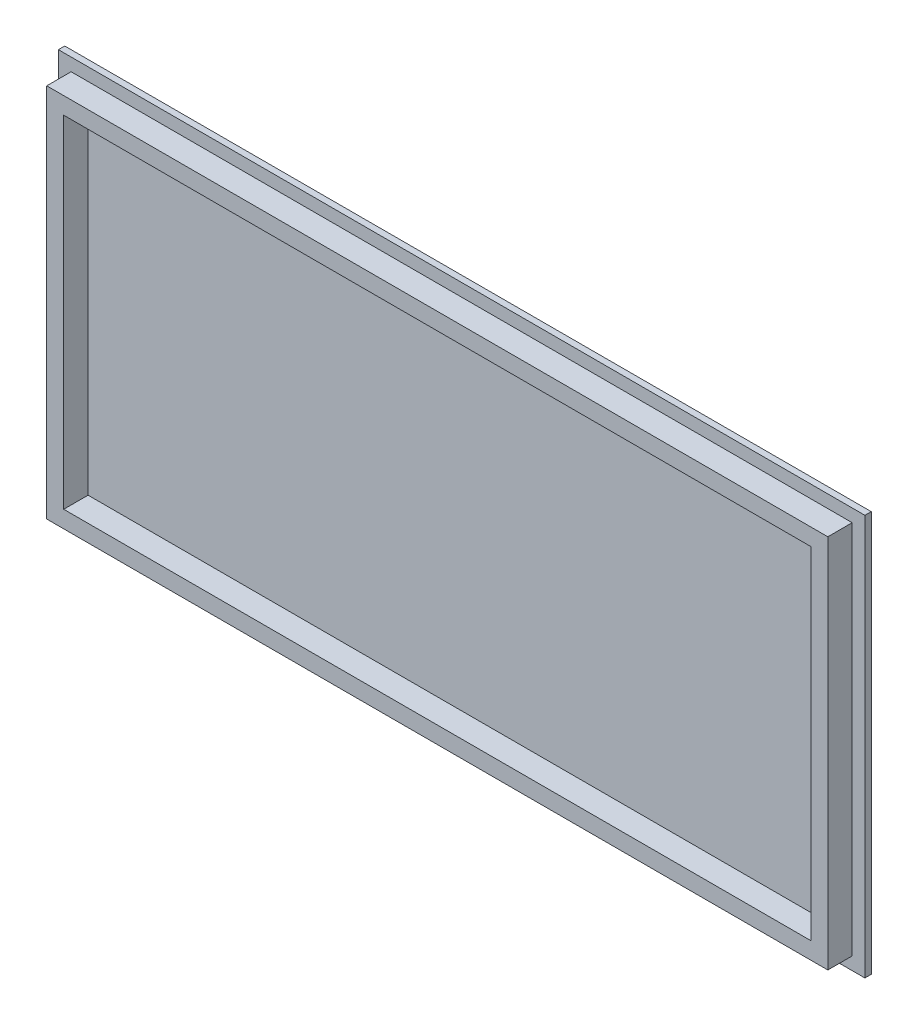
SolidWorks part; units mm, degrees
ref_plane "Front Plane" through (0, 0, 0) normal (0, 0, 1) x (1, 0, 0)
ref_plane "Top Plane" through (0, 0, 0) normal (0, 1, 0) x (1, 0, 0)
ref_plane "Right Plane" through (0, 0, 0) normal (1, 0, 0) x (0, 0, -1)
sketch "Model" plane through (0, 0, 0) normal (0, 0, 1) x (1, 0, 0)
  line L0 (3.8158, 5.1291) -> (3.565, 5.0023)
  line L1 (3.565, 5.0023) -> (3.3652, 4.8038)
  line L2 (3.3652, 4.8038) -> (3.2384, 4.5531)
  line L3 (3.2384, 4.5531) -> (3.1943, 4.2733)
  line L4 (3.1943, 4.2733) -> (3.2384, 3.9949)
  line L5 (3.2384, 3.9949) -> (3.3652, 3.7441)
  line L6 (3.3652, 3.7441) -> (3.565, 3.5457)
  line L7 (3.565, 3.5457) -> (3.8158, 3.4189)
  line L8 (3.8158, 3.4189) -> (4.0942, 3.3734)
  line L9 (4.0942, 3.3734) -> (4.3725, 3.4189)
  line L10 (4.3725, 3.4189) -> (4.6233, 3.5457)
  line L11 (4.6233, 3.5457) -> (4.8231, 3.7441)
  line L12 (4.8231, 3.7441) -> (4.9499, 3.9949)
  line L13 (4.9499, 3.9949) -> (4.994, 4.2733)
  line L14 (4.994, 4.2733) -> (4.9499, 4.5531)
  line L15 (4.9499, 4.5531) -> (4.8231, 4.8038)
  line L16 (4.8231, 4.8038) -> (4.6233, 5.0023)
  line L17 (4.6233, 5.0023) -> (4.3725, 5.1291)
  line L18 (4.3725, 5.1291) -> (4.0942, 5.1732)
  line L19 (4.0942, 5.1732) -> (3.8158, 5.1291)
  line L20 (75.7107, 5.1291) -> (75.4599, 5.0023)
  line L21 (75.4599, 5.0023) -> (75.2602, 4.8038)
  line L22 (75.2602, 4.8038) -> (75.1321, 4.5531)
  line L23 (75.1321, 4.5531) -> (75.088, 4.2733)
  line L24 (75.088, 4.2733) -> (75.1321, 3.9949)
  line L25 (75.1321, 3.9949) -> (75.2602, 3.7441)
  line L26 (75.2602, 3.7441) -> (75.4599, 3.5457)
  line L27 (75.4599, 3.5457) -> (75.7107, 3.4189)
  line L28 (75.7107, 3.4189) -> (75.989, 3.3734)
  line L29 (75.989, 3.3734) -> (76.2663, 3.4189)
  line L30 (76.2663, 3.4189) -> (76.5168, 3.5457)
  line L31 (76.5168, 3.5457) -> (76.7168, 3.7441)
  line L32 (76.7168, 3.7441) -> (76.8449, 3.9949)
  line L33 (76.8449, 3.9949) -> (76.889, 4.2733)
  line L34 (76.889, 4.2733) -> (76.8449, 4.5531)
  line L35 (76.8449, 4.5531) -> (76.7168, 4.8038)
  line L36 (76.7168, 4.8038) -> (76.5168, 5.0023)
  line L37 (76.5168, 5.0023) -> (76.2663, 5.1291)
  line L38 (76.2663, 5.1291) -> (75.989, 5.1732)
  line L39 (75.989, 5.1732) -> (75.7107, 5.1291)
  line L40 (147.606, 5.1291) -> (147.355, 5.0023)
  line L41 (147.355, 5.0023) -> (147.155, 4.8038)
  line L42 (147.155, 4.8038) -> (147.027, 4.5531)
  line L43 (147.027, 4.5531) -> (146.983, 4.2733)
  line L44 (146.983, 4.2733) -> (147.027, 3.9949)
  line L45 (147.027, 3.9949) -> (147.155, 3.7441)
  line L46 (147.155, 3.7441) -> (147.355, 3.5457)
  line L47 (147.355, 3.5457) -> (147.606, 3.4189)
  line L48 (147.606, 3.4189) -> (147.884, 3.3734)
  line L49 (147.884, 3.3734) -> (148.161, 3.4189)
  line L50 (148.161, 3.4189) -> (148.412, 3.5457)
  line L51 (148.412, 3.5457) -> (148.612, 3.7441)
  line L52 (148.612, 3.7441) -> (148.74, 3.9949)
  line L53 (148.74, 3.9949) -> (148.784, 4.2733)
  line L54 (148.784, 4.2733) -> (148.74, 4.5531)
  line L55 (148.74, 4.5531) -> (148.612, 4.8038)
  line L56 (148.612, 4.8038) -> (148.412, 5.0023)
  line L57 (148.412, 5.0023) -> (148.161, 5.1291)
  line L58 (148.161, 5.1291) -> (147.884, 5.1732)
  line L59 (147.884, 5.1732) -> (147.606, 5.1291)
  line L60 (219.499, 5.1291) -> (219.25, 5.0023)
  line L61 (219.25, 5.0023) -> (219.049, 4.8038)
  line L62 (219.049, 4.8038) -> (218.922, 4.5531)
  line L63 (218.922, 4.5531) -> (218.878, 4.2733)
  line L64 (218.878, 4.2733) -> (218.922, 3.9949)
  line L65 (218.922, 3.9949) -> (219.049, 3.7441)
  line L66 (219.049, 3.7441) -> (219.25, 3.5457)
  line L67 (219.25, 3.5457) -> (219.499, 3.4189)
  line L68 (219.499, 3.4189) -> (219.778, 3.3734)
  line L69 (219.778, 3.3734) -> (220.056, 3.4189)
  line L70 (220.056, 3.4189) -> (220.307, 3.5457)
  line L71 (220.307, 3.5457) -> (220.507, 3.7441)
  line L72 (220.507, 3.7441) -> (220.635, 3.9949)
  line L73 (220.635, 3.9949) -> (220.679, 4.2733)
  line L74 (220.679, 4.2733) -> (220.635, 4.5531)
  line L75 (220.635, 4.5531) -> (220.507, 4.8038)
  line L76 (220.507, 4.8038) -> (220.307, 5.0023)
  line L77 (220.307, 5.0023) -> (220.056, 5.1291)
  line L78 (220.056, 5.1291) -> (219.778, 5.1732)
  line L79 (219.778, 5.1732) -> (219.499, 5.1291)
  line L80 (291.394, 5.1291) -> (291.144, 5.0023)
  line L81 (291.144, 5.0023) -> (290.944, 4.8038)
  line L82 (290.944, 4.8038) -> (290.817, 4.5531)
  line L83 (290.817, 4.5531) -> (290.773, 4.2733)
  line L84 (290.773, 4.2733) -> (290.817, 3.9949)
  line L85 (290.817, 3.9949) -> (290.944, 3.7441)
  line L86 (290.944, 3.7441) -> (291.144, 3.5457)
  line L87 (291.144, 3.5457) -> (291.394, 3.4189)
  line L88 (291.394, 3.4189) -> (291.673, 3.3734)
  line L89 (291.673, 3.3734) -> (291.95, 3.4189)
  line L90 (291.95, 3.4189) -> (292.202, 3.5457)
  line L91 (292.202, 3.5457) -> (292.401, 3.7441)
  line L92 (292.401, 3.7441) -> (292.529, 3.9949)
  line L93 (292.529, 3.9949) -> (292.573, 4.2733)
  line L94 (292.573, 4.2733) -> (292.529, 4.5531)
  line L95 (292.529, 4.5531) -> (292.401, 4.8038)
  line L96 (292.401, 4.8038) -> (292.202, 5.0023)
  line L97 (292.202, 5.0023) -> (291.95, 5.1291)
  line L98 (291.95, 5.1291) -> (291.673, 5.1732)
  line L99 (291.673, 5.1732) -> (291.394, 5.1291)
  line L100 (363.291, 5.1291) -> (363.04, 5.0023)
  line L101 (363.04, 5.0023) -> (362.839, 4.8038)
  line L102 (362.839, 4.8038) -> (362.712, 4.5531)
  line L103 (362.712, 4.5531) -> (362.67, 4.2733)
  line L104 (362.67, 4.2733) -> (362.712, 3.9949)
  line L105 (362.712, 3.9949) -> (362.839, 3.7441)
  line L106 (362.839, 3.7441) -> (363.04, 3.5457)
  line L107 (363.04, 3.5457) -> (363.291, 3.4189)
  line L108 (363.291, 3.4189) -> (363.569, 3.3734)
  line L109 (363.569, 3.3734) -> (363.844, 3.4189)
  line L110 (363.844, 3.4189) -> (364.098, 3.5457)
  line L111 (364.098, 3.5457) -> (364.296, 3.7441)
  line L112 (364.296, 3.7441) -> (364.423, 3.9949)
  line L113 (364.423, 3.9949) -> (364.469, 4.2733)
  line L114 (364.469, 4.2733) -> (364.423, 4.5531)
  line L115 (364.423, 4.5531) -> (364.296, 4.8038)
  line L116 (364.296, 4.8038) -> (364.098, 5.0023)
  line L117 (364.098, 5.0023) -> (363.844, 5.1291)
  line L118 (363.844, 5.1291) -> (363.569, 5.1732)
  line L119 (363.569, 5.1732) -> (363.291, 5.1291)
  line L120 (131.917, 27.3251) -> (189.071, 27.3251)
  line L121 (189.071, 27.3251) -> (189.071, 8.2737)
  line L122 (189.071, 8.2737) -> (131.917, 8.2737)
  line L123 (131.917, 8.2737) -> (131.917, 27.3251)
  line L124 (250.028, 142.579) -> (250.028, 123.963)
  line L125 (250.028, 123.963) -> (246.976, 138.322)
  line L126 (246.976, 138.322) -> (228.342, 134.36)
  line L127 (228.342, 134.36) -> (228.342, 134.361)
  line L128 (228.342, 134.361) -> (209.708, 130.4)
  line L129 (209.708, 130.4) -> (209.708, 130.401)
  line L130 (209.708, 130.401) -> (172.44, 122.479)
  line L131 (172.44, 122.479) -> (176.4, 103.845)
  line L132 (176.4, 103.845) -> (167.083, 101.865)
  line L133 (167.083, 101.865) -> (171.045, 83.228)
  line L134 (171.045, 83.228) -> (175.703, 84.2186)
  line L135 (175.703, 84.2186) -> (179.663, 65.5863)
  line L136 (179.663, 65.5863) -> (165.687, 62.6166)
  line L137 (165.687, 62.6166) -> (169.649, 43.9801)
  line L138 (169.649, 43.9801) -> (178.966, 45.9617)
  line L139 (178.966, 45.9617) -> (182.926, 27.3279)
  line L140 (182.926, 27.3279) -> (243.487, 40.2001)
  line L141 (243.487, 40.2001) -> (243.487, 40.1987)
  line L142 (243.487, 40.1987) -> (266.78, 45.1513)
  line L143 (266.78, 45.1513) -> (258.859, 82.4205)
  line L144 (258.859, 82.4205) -> (254.2, 81.431)
  line L145 (254.2, 81.431) -> (250.241, 100.062)
  line L146 (250.241, 100.062) -> (254.791, 101.03)
  line L147 (254.791, 101.03) -> (254.791, 82.568)
  line L148 (254.791, 82.568) -> (264.316, 82.568)
  line L149 (264.316, 82.568) -> (264.316, 63.518)
  line L150 (264.316, 63.518) -> (270.031, 63.518)
  line L151 (270.031, 63.518) -> (270.031, 44.468)
  line L152 (270.031, 44.468) -> (293.846, 44.468)
  line L153 (293.846, 44.468) -> (293.846, 63.518)
  line L154 (293.846, 63.518) -> (316.705, 63.518)
  line L155 (316.705, 63.518) -> (316.705, 82.568)
  line L156 (316.705, 82.568) -> (335.755, 82.568)
  line L157 (335.755, 82.568) -> (335.755, 101.621)
  line L158 (335.755, 101.621) -> (330.992, 101.621)
  line L159 (330.992, 101.621) -> (330.992, 120.671)
  line L160 (330.992, 120.671) -> (326.23, 120.671)
  line L161 (326.23, 120.671) -> (326.23, 139.721)
  line L162 (326.23, 139.721) -> (269.08, 139.721)
  line L163 (269.08, 139.721) -> (269.08, 142.579)
  line L164 (269.08, 142.579) -> (250.028, 142.579)
  line L165 (79.6452, 120.831) -> (70.327, 122.811)
  line L166 (70.327, 122.811) -> (66.3663, 104.176)
  line L167 (66.3663, 104.176) -> (71.0255, 103.185)
  line L168 (71.0255, 103.185) -> (67.0648, 84.551)
  line L169 (67.0648, 84.551) -> (76.382, 82.5722)
  line L170 (76.382, 82.5722) -> (72.42, 63.9367)
  line L171 (72.42, 63.9367) -> (72.4214, 63.9367)
  line L172 (72.4214, 63.9367) -> (68.4597, 45.303)
  line L173 (68.4597, 45.303) -> (133.679, 31.4399)
  line L174 (133.679, 31.4399) -> (133.679, 31.4413)
  line L175 (133.679, 31.4413) -> (152.313, 27.4808)
  line L176 (152.313, 27.4808) -> (156.275, 46.1162)
  line L177 (156.275, 46.1162) -> (146.958, 48.0949)
  line L178 (146.958, 48.0949) -> (150.919, 66.7286)
  line L179 (150.919, 66.7286) -> (141.602, 68.7091)
  line L180 (141.602, 68.7091) -> (145.562, 87.3428)
  line L181 (145.562, 87.3428) -> (140.903, 88.3338)
  line L182 (140.903, 88.3338) -> (144.865, 106.966)
  line L183 (144.865, 106.966) -> (154.182, 104.986)
  line L184 (154.182, 104.986) -> (158.142, 123.621)
  line L185 (158.142, 123.621) -> (139.507, 127.583)
  line L186 (139.507, 127.583) -> (139.507, 127.581)
  line L187 (139.507, 127.581) -> (83.6055, 139.464)
  line L188 (83.6055, 139.464) -> (79.6452, 120.831)
  line L189 (321.466, 77.8083) -> (321.466, 58.7583)
  line L190 (321.466, 58.7583) -> (302.416, 58.7583)
  line L191 (302.416, 58.7583) -> (302.416, 39.7069)
  line L192 (302.416, 39.7069) -> (359.569, 39.7069)
  line L193 (359.569, 39.7069) -> (359.569, 58.7583)
  line L194 (359.569, 58.7583) -> (340.517, 58.7583)
  line L195 (340.517, 58.7583) -> (340.517, 77.8083)
  line L196 (340.517, 77.8083) -> (321.466, 77.8083)
  line L197 (60.4795, 142.579) -> (60.4795, 139.721)
  line L198 (60.4795, 139.721) -> (22.3807, 139.721)
  line L199 (22.3807, 139.721) -> (22.3807, 120.671)
  line L200 (22.3807, 120.671) -> (17.6182, 120.671)
  line L201 (17.6182, 120.671) -> (17.6182, 101.621)
  line L202 (17.6182, 101.621) -> (12.8557, 101.621)
  line L203 (12.8557, 101.621) -> (12.8557, 82.5708)
  line L204 (12.8557, 82.5708) -> (8.0932, 82.5708)
  line L205 (8.0932, 82.5708) -> (8.0932, 44.468)
  line L206 (8.0932, 44.468) -> (60.482, 44.468)
  line L207 (60.482, 44.468) -> (60.482, 63.518)
  line L208 (60.482, 63.518) -> (70.007, 63.518)
  line L209 (70.007, 63.518) -> (70.007, 82.5708)
  line L210 (70.007, 82.5708) -> (65.2459, 82.5708)
  line L211 (65.2459, 82.5708) -> (65.2459, 120.671)
  line L212 (65.2459, 120.671) -> (60.482, 120.671)
  line L213 (60.482, 120.671) -> (60.482, 123.526)
  line L214 (60.482, 123.526) -> (79.532, 123.526)
  line L215 (79.532, 123.526) -> (79.532, 142.579)
  line L216 (79.532, 142.579) -> (60.4795, 142.579)
  line L217 (326.227, 163.533) -> (326.227, 144.482)
  line L218 (326.227, 144.482) -> (330.991, 144.482)
  line L219 (330.991, 144.482) -> (330.991, 125.432)
  line L220 (330.991, 125.432) -> (335.753, 125.432)
  line L221 (335.753, 125.432) -> (335.753, 106.382)
  line L222 (335.753, 106.382) -> (340.516, 106.382)
  line L223 (340.516, 106.382) -> (340.516, 87.3319)
  line L224 (340.516, 87.3319) -> (359.569, 87.3319)
  line L225 (359.569, 87.3319) -> (359.569, 106.383)
  line L226 (359.569, 106.383) -> (354.806, 106.383)
  line L227 (354.806, 106.383) -> (354.806, 125.433)
  line L228 (354.806, 125.433) -> (350.042, 125.433)
  line L229 (350.042, 125.433) -> (350.042, 144.483)
  line L230 (350.042, 144.483) -> (345.28, 144.483)
  line L231 (345.28, 144.483) -> (345.28, 163.533)
  line L232 (345.28, 163.533) -> (326.227, 163.533)
  line L233 (3.8158, 89.1399) -> (3.565, 89.0129)
  line L234 (3.565, 89.0129) -> (3.3652, 88.8132)
  line L235 (3.3652, 88.8132) -> (3.2384, 88.5624)
  line L236 (3.2384, 88.5624) -> (3.1943, 88.284)
  line L237 (3.1943, 88.284) -> (3.2384, 88.0071)
  line L238 (3.2384, 88.0071) -> (3.3652, 87.7549)
  line L239 (3.3652, 87.7549) -> (3.565, 87.5563)
  line L240 (3.565, 87.5563) -> (3.8158, 87.4282)
  line L241 (3.8158, 87.4282) -> (4.0942, 87.3841)
  line L242 (4.0942, 87.3841) -> (4.3725, 87.4282)
  line L243 (4.3725, 87.4282) -> (4.6233, 87.5563)
  line L244 (4.6233, 87.5563) -> (4.8231, 87.7549)
  line L245 (4.8231, 87.7549) -> (4.9499, 88.0071)
  line L246 (4.9499, 88.0071) -> (4.994, 88.284)
  line L247 (4.994, 88.284) -> (4.9499, 88.5624)
  line L248 (4.9499, 88.5624) -> (4.8231, 88.8132)
  line L249 (4.8231, 88.8132) -> (4.6233, 89.0129)
  line L250 (4.6233, 89.0129) -> (4.3725, 89.1399)
  line L251 (4.3725, 89.1399) -> (4.0942, 89.184)
  line L252 (4.0942, 89.184) -> (3.8158, 89.1399)
  line L253 (363.291, 89.1399) -> (363.04, 89.0129)
  line L254 (363.04, 89.0129) -> (362.839, 88.8132)
  line L255 (362.839, 88.8132) -> (362.712, 88.5624)
  line L256 (362.712, 88.5624) -> (362.67, 88.284)
  line L257 (362.67, 88.284) -> (362.712, 88.0071)
  line L258 (362.712, 88.0071) -> (362.839, 87.7549)
  line L259 (362.839, 87.7549) -> (363.04, 87.5563)
  line L260 (363.04, 87.5563) -> (363.291, 87.4282)
  line L261 (363.291, 87.4282) -> (363.569, 87.3841)
  line L262 (363.569, 87.3841) -> (363.844, 87.4282)
  line L263 (363.844, 87.4282) -> (364.098, 87.5563)
  line L264 (364.098, 87.5563) -> (364.296, 87.7549)
  line L265 (364.296, 87.7549) -> (364.423, 88.0071)
  line L266 (364.423, 88.0071) -> (364.469, 88.284)
  line L267 (364.469, 88.284) -> (364.423, 88.5624)
  line L268 (364.423, 88.5624) -> (364.296, 88.8132)
  line L269 (364.296, 88.8132) -> (364.098, 89.0129)
  line L270 (364.098, 89.0129) -> (363.844, 89.1399)
  line L271 (363.844, 89.1399) -> (363.569, 89.184)
  line L272 (363.569, 89.184) -> (363.291, 89.1399)
  line L273 (269.078, 120.671) -> (264.316, 120.671)
  line L274 (264.316, 120.671) -> (264.316, 101.621)
  line L275 (264.316, 101.621) -> (257.572, 101.621)
  line L276 (257.572, 101.621) -> (264.214, 103.032)
  line L277 (264.214, 103.032) -> (260.254, 121.668)
  line L278 (260.254, 121.668) -> (250.938, 119.688)
  line L279 (250.938, 119.688) -> (250.121, 123.526)
  line L280 (250.121, 123.526) -> (269.078, 123.526)
  line L281 (269.078, 123.526) -> (269.078, 120.671)
  line L282 (172.146, 146.761) -> (176.109, 128.126)
  line L283 (176.109, 128.126) -> (194.741, 132.086)
  line L284 (194.741, 132.086) -> (194.741, 132.085)
  line L285 (194.741, 132.085) -> (213.377, 136.047)
  line L286 (213.377, 136.047) -> (209.416, 154.682)
  line L287 (209.416, 154.682) -> (172.146, 146.761)
  line L288 (117.205, 137.189) -> (154.474, 129.267)
  line L289 (154.474, 129.267) -> (158.434, 147.903)
  line L290 (158.434, 147.903) -> (121.165, 155.826)
  line L291 (121.165, 155.826) -> (117.205, 137.189)
  line L292 (214.073, 155.673) -> (218.033, 137.036)
  line L293 (218.033, 137.036) -> (255.304, 144.959)
  line L294 (255.304, 144.959) -> (251.343, 163.594)
  line L295 (251.343, 163.594) -> (214.073, 155.673)
  line L296 (75.2782, 146.101) -> (112.547, 138.18)
  line L297 (112.547, 138.18) -> (116.509, 156.815)
  line L298 (116.509, 156.815) -> (97.874, 160.776)
  line L299 (97.874, 160.776) -> (79.2399, 164.736)
  line L300 (79.2399, 164.736) -> (75.2782, 146.101)
  line L301 (300.797, 163.533) -> (319.848, 163.533)
  line L302 (319.848, 163.533) -> (319.848, 144.482)
  line L303 (319.848, 144.482) -> (300.797, 144.482)
  line L304 (300.797, 144.482) -> (300.797, 163.533)
  line L305 (11.9035, 163.533) -> (30.9549, 163.533)
  line L306 (30.9549, 163.533) -> (30.9549, 144.482)
  line L307 (30.9549, 144.482) -> (11.9035, 144.482)
  line L308 (11.9035, 144.482) -> (11.9035, 163.533)
  line L309 (255.743, 164.485) -> (293.846, 164.485)
  line L310 (293.846, 164.485) -> (293.846, 145.434)
  line L311 (293.846, 145.434) -> (255.743, 145.434)
  line L312 (255.743, 145.434) -> (255.743, 164.485)
  line L313 (36.6681, 164.485) -> (74.7709, 164.485)
  line L314 (74.7709, 164.485) -> (74.7709, 145.434)
  line L315 (74.7709, 145.434) -> (36.6681, 145.434)
  line L316 (36.6681, 145.434) -> (36.6681, 164.485)
  line L317 (3.8158, 173.15) -> (3.565, 173.024)
  line L318 (3.565, 173.024) -> (3.3652, 172.824)
  line L319 (3.3652, 172.824) -> (3.2384, 172.573)
  line L320 (3.2384, 172.573) -> (3.1943, 172.295)
  line L321 (3.1943, 172.295) -> (3.2384, 172.016)
  line L322 (3.2384, 172.016) -> (3.3652, 171.766)
  line L323 (3.3652, 171.766) -> (3.565, 171.566)
  line L324 (3.565, 171.566) -> (3.8158, 171.439)
  line L325 (3.8158, 171.439) -> (4.0942, 171.395)
  line L326 (4.0942, 171.395) -> (4.3725, 171.439)
  line L327 (4.3725, 171.439) -> (4.6233, 171.566)
  line L328 (4.6233, 171.566) -> (4.8231, 171.766)
  line L329 (4.8231, 171.766) -> (4.9499, 172.016)
  line L330 (4.9499, 172.016) -> (4.994, 172.295)
  line L331 (4.994, 172.295) -> (4.9499, 172.573)
  line L332 (4.9499, 172.573) -> (4.8231, 172.824)
  line L333 (4.8231, 172.824) -> (4.6233, 173.024)
  line L334 (4.6233, 173.024) -> (4.3725, 173.15)
  line L335 (4.3725, 173.15) -> (4.0942, 173.194)
  line L336 (4.0942, 173.194) -> (3.8158, 173.15)
  line L337 (363.291, 173.15) -> (363.04, 173.024)
  line L338 (363.04, 173.024) -> (362.839, 172.824)
  line L339 (362.839, 172.824) -> (362.712, 172.573)
  line L340 (362.712, 172.573) -> (362.67, 172.295)
  line L341 (362.67, 172.295) -> (362.712, 172.016)
  line L342 (362.712, 172.016) -> (362.839, 171.766)
  line L343 (362.839, 171.766) -> (363.04, 171.566)
  line L344 (363.04, 171.566) -> (363.291, 171.439)
  line L345 (363.291, 171.439) -> (363.569, 171.395)
  line L346 (363.569, 171.395) -> (363.844, 171.439)
  line L347 (363.844, 171.439) -> (364.098, 171.566)
  line L348 (364.098, 171.566) -> (364.296, 171.766)
  line L349 (364.296, 171.766) -> (364.423, 172.016)
  line L350 (364.423, 172.016) -> (364.469, 172.295)
  line L351 (364.469, 172.295) -> (364.423, 172.573)
  line L352 (364.423, 172.573) -> (364.296, 172.824)
  line L353 (364.296, 172.824) -> (364.098, 173.024)
  line L354 (364.098, 173.024) -> (363.844, 173.15)
  line L355 (363.844, 173.15) -> (363.569, 173.194)
  line L356 (363.569, 173.194) -> (363.291, 173.15)
  line L357 (291.394, 173.15) -> (291.144, 173.024)
  line L358 (291.144, 173.024) -> (290.944, 172.824)
  line L359 (290.944, 172.824) -> (290.817, 172.573)
  line L360 (290.817, 172.573) -> (290.773, 172.295)
  line L361 (290.773, 172.295) -> (290.817, 172.016)
  line L362 (290.817, 172.016) -> (290.944, 171.766)
  line L363 (290.944, 171.766) -> (291.144, 171.566)
  line L364 (291.144, 171.566) -> (291.394, 171.439)
  line L365 (291.394, 171.439) -> (291.673, 171.395)
  line L366 (291.673, 171.395) -> (291.95, 171.439)
  line L367 (291.95, 171.439) -> (292.202, 171.566)
  line L368 (292.202, 171.566) -> (292.401, 171.766)
  line L369 (292.401, 171.766) -> (292.529, 172.016)
  line L370 (292.529, 172.016) -> (292.573, 172.295)
  line L371 (292.573, 172.295) -> (292.529, 172.573)
  line L372 (292.529, 172.573) -> (292.401, 172.824)
  line L373 (292.401, 172.824) -> (292.202, 173.024)
  line L374 (292.202, 173.024) -> (291.95, 173.15)
  line L375 (291.95, 173.15) -> (291.673, 173.194)
  line L376 (291.673, 173.194) -> (291.394, 173.15)
  line L377 (219.499, 173.15) -> (219.25, 173.024)
  line L378 (219.25, 173.024) -> (219.049, 172.824)
  line L379 (219.049, 172.824) -> (218.922, 172.573)
  line L380 (218.922, 172.573) -> (218.878, 172.295)
  line L381 (218.878, 172.295) -> (218.922, 172.016)
  line L382 (218.922, 172.016) -> (219.049, 171.766)
  line L383 (219.049, 171.766) -> (219.25, 171.566)
  line L384 (219.25, 171.566) -> (219.499, 171.439)
  line L385 (219.499, 171.439) -> (219.778, 171.395)
  line L386 (219.778, 171.395) -> (220.056, 171.439)
  line L387 (220.056, 171.439) -> (220.307, 171.566)
  line L388 (220.307, 171.566) -> (220.507, 171.766)
  line L389 (220.507, 171.766) -> (220.635, 172.016)
  line L390 (220.635, 172.016) -> (220.679, 172.295)
  line L391 (220.679, 172.295) -> (220.635, 172.573)
  line L392 (220.635, 172.573) -> (220.507, 172.824)
  line L393 (220.507, 172.824) -> (220.307, 173.024)
  line L394 (220.307, 173.024) -> (220.056, 173.15)
  line L395 (220.056, 173.15) -> (219.778, 173.194)
  line L396 (219.778, 173.194) -> (219.499, 173.15)
  line L397 (147.606, 173.15) -> (147.355, 173.024)
  line L398 (147.355, 173.024) -> (147.155, 172.824)
  line L399 (147.155, 172.824) -> (147.027, 172.573)
  line L400 (147.027, 172.573) -> (146.983, 172.295)
  line L401 (146.983, 172.295) -> (147.027, 172.016)
  line L402 (147.027, 172.016) -> (147.155, 171.766)
  line L403 (147.155, 171.766) -> (147.355, 171.566)
  line L404 (147.355, 171.566) -> (147.606, 171.439)
  line L405 (147.606, 171.439) -> (147.884, 171.395)
  line L406 (147.884, 171.395) -> (148.161, 171.439)
  line L407 (148.161, 171.439) -> (148.412, 171.566)
  line L408 (148.412, 171.566) -> (148.612, 171.766)
  line L409 (148.612, 171.766) -> (148.74, 172.016)
  line L410 (148.74, 172.016) -> (148.784, 172.295)
  line L411 (148.784, 172.295) -> (148.74, 172.573)
  line L412 (148.74, 172.573) -> (148.612, 172.824)
  line L413 (148.612, 172.824) -> (148.412, 173.024)
  line L414 (148.412, 173.024) -> (148.161, 173.15)
  line L415 (148.161, 173.15) -> (147.884, 173.194)
  line L416 (147.884, 173.194) -> (147.606, 173.15)
  line L417 (75.7107, 173.15) -> (75.4599, 173.024)
  line L418 (75.4599, 173.024) -> (75.2602, 172.824)
  line L419 (75.2602, 172.824) -> (75.1321, 172.573)
  line L420 (75.1321, 172.573) -> (75.088, 172.295)
  line L421 (75.088, 172.295) -> (75.1321, 172.016)
  line L422 (75.1321, 172.016) -> (75.2602, 171.766)
  line L423 (75.2602, 171.766) -> (75.4599, 171.566)
  line L424 (75.4599, 171.566) -> (75.7107, 171.439)
  line L425 (75.7107, 171.439) -> (75.989, 171.395)
  line L426 (75.989, 171.395) -> (76.2663, 171.439)
  line L427 (76.2663, 171.439) -> (76.5168, 171.566)
  line L428 (76.5168, 171.566) -> (76.7168, 171.766)
  line L429 (76.7168, 171.766) -> (76.8449, 172.016)
  line L430 (76.8449, 172.016) -> (76.889, 172.295)
  line L431 (76.889, 172.295) -> (76.8449, 172.573)
  line L432 (76.8449, 172.573) -> (76.7168, 172.824)
  line L433 (76.7168, 172.824) -> (76.5168, 173.024)
  line L434 (76.5168, 173.024) -> (76.2663, 173.15)
  line L435 (76.2663, 173.15) -> (75.989, 173.194)
  line L436 (75.989, 173.194) -> (75.7107, 173.15)
  line L437 (-7.9049, -7.7268) -> (-7.9354, 184.294)
  line L438 (-7.9354, 184.294) -> (375.4737, 184.294)
  line L439 (375.4737, 184.294) -> (375.566, -7.7437)
  line L440 (375.566, -7.7437) -> (-7.9049, -7.7268)
  line L441 (-0.4014, 176.794) -> (368.0633, 176.794)
  line L442 (-0.4101, -0.2271) -> (-0.4014, 176.794)
  line L443 (368.066, -0.2208) -> (-0.4101, -0.2271)
  line L444 (368.0633, 176.794) -> (368.066, -0.2208)
sketch "草图2" plane through (0, 0, 0) normal (0, 0, 1) x (1, 0, 0)
  line L0 (-7.9354, 184.294) -> (375.566, -7.7437) construction
  line L1 (-6.4197, -6.2448) -> (-6.4197, 182.7952)
  line L2 (375.5503, -7.7448) -> (-7.9197, -7.7448)
  line L3 (375.5503, -7.7448) -> (375.5503, 184.2952)
  line L4 (375.5503, 184.2952) -> (-7.9197, 184.2952)
  line L5 (-7.9197, -7.7448) -> (-7.9197, 184.2952)
  line L6 (375.5503, -7.7448) -> (-7.9197, 184.2952) construction
  line L7 (375.5503, 184.2952) -> (-7.9197, -7.7448) construction
  line L8 (374.0503, 182.7952) -> (-6.4197, 182.7952)
  line L9 (374.0503, -6.2448) -> (374.0503, 182.7952)
  line L10 (374.0503, -6.2448) -> (-6.4197, -6.2448)
  point P4 (183.8153, 88.2752)
  dimension "D1" = 383.47
  dimension "D2" = 192.04
  dimension "D3" = 1.5
extrude "凸台-拉伸1" add sketch "草图2" along normal blind 3 contours L1 L8 L9 L10
sketch "草图3" plane through (0, 0, 3) normal (0, 0, 1) x (1, 0, 0)
  line L1 (368.0553, -0.2298) -> (-0.4247, -0.2298)
  line L2 (368.0553, -0.2298) -> (368.0553, 176.7802)
  line L3 (368.0553, 176.7802) -> (-0.4247, 176.7802)
  line L4 (-0.4247, -0.2298) -> (-0.4247, 176.7802)
  line L5 (368.0553, -0.2298) -> (-0.4247, 176.7802) construction
  line L6 (368.0553, 176.7802) -> (-0.4247, -0.2298) construction
  point P0 (183.8153, 88.2752)
  dimension "D1" = 368.48
  dimension "D2" = 177.01
extrude "凸台-拉伸2" add sketch "草图3" along normal blind 11.5
sketch "草图4" plane through (0, 0, 14.5) normal (0, 0, 1) x (1, 0, 0)
  line L8 (7.5753, 168.7802) -> (7.5753, 7.7702)
  line L9 (7.5753, 7.7702) -> (360.0553, 7.7702)
  line L10 (360.0553, 7.7702) -> (360.0553, 168.7802)
  line L11 (360.0553, 168.7802) -> (7.5753, 168.7802)
  line L12 (7.5753, 168.7802) -> (7.5753, 7.7702)
  line L13 (7.5753, 7.7702) -> (360.0553, 7.7702)
  line L14 (360.0553, 7.7702) -> (360.0553, 168.7802)
  line L15 (360.0553, 168.7802) -> (7.5753, 168.7802)
  dimension "D1" = 8
extrude "切除-拉伸1" cut sketch "草图4" against normal blind 11.5
